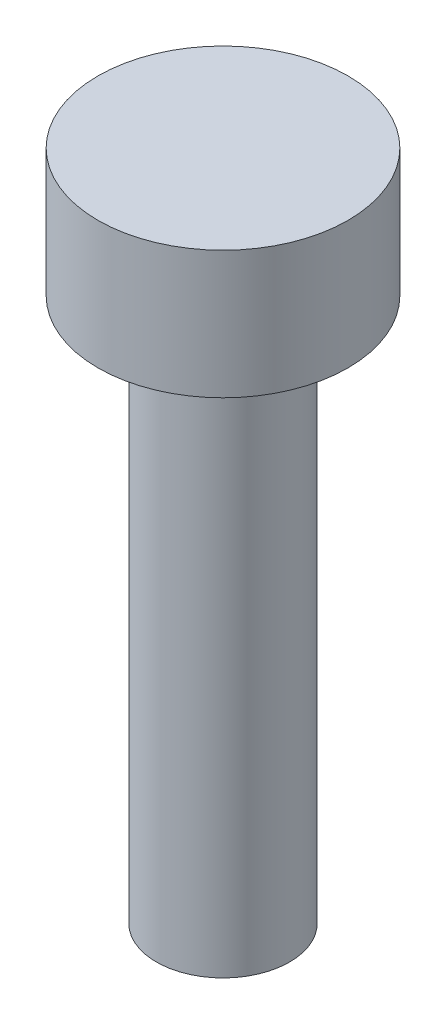
SolidWorks part; units mm, degrees
ref_plane "Front Plane" through (0, 0, 0) normal (0, 0, 1) x (1, 0, 0)
ref_plane "Top Plane" through (0, 0, 0) normal (0, 1, 0) x (1, 0, 0)
ref_plane "Right Plane" through (0, 0, 0) normal (1, 0, 0) x (0, 0, -1)
sketch "Sketch1" plane through (0, 0, 0) normal (0, 1, 0) x (1, 0, 0)
  circle A0 centre (0, 0) radius 1.84
  dimension "D1" = 3.68
extrude "Boss-Extrude1" add sketch "Sketch1" along normal blind 1.88
sketch "Sketch2" plane through (0, 0, 0) normal (0, -1, 0) x (1, 0, 0)
  circle A0 centre (0, 0) radius 0.98
  dimension "D1" = 1.96
extrude "Boss-Extrude2" add sketch "Sketch2" along normal blind 8
